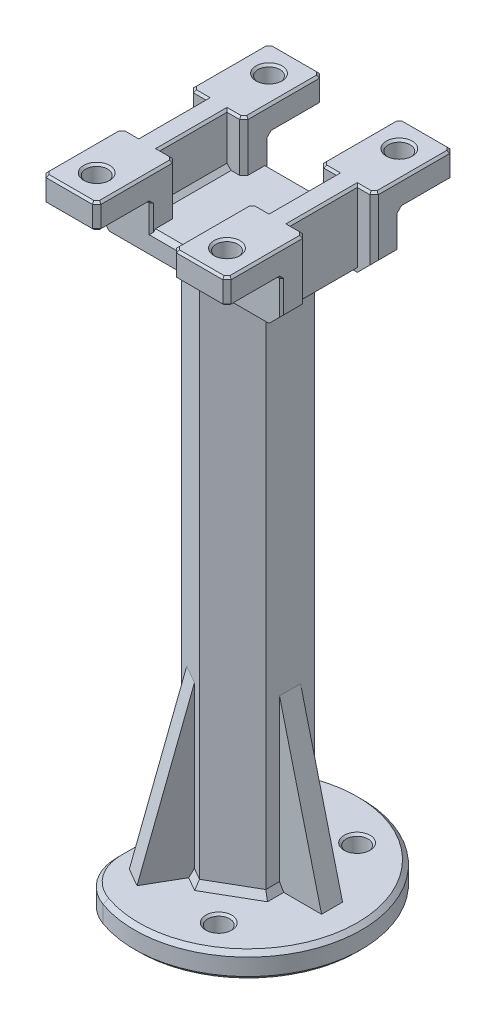
SolidWorks part; units mm, degrees
material "PET"
ref_plane "Front Plane" through (0, 0, 0) normal (0, 0, 1) x (1, 0, 0)
ref_plane "Top Plane" through (0, 0, 0) normal (0, 1, 0) x (1, 0, 0)
ref_plane "Right Plane" through (0, 0, 0) normal (1, 0, 0) x (0, 0, -1)
sketch "Sketch3" plane through (0, 0, 0) normal (0, 1, 0) x (1, 0, 0)
  circle A0 centre (0, 0) radius 27
  dimension "D1" = 54
extrude "Boss-Extrude1" add sketch "Sketch3" along normal blind 6
sketch "Sketch4" plane through (0, 6, 0) normal (0, 1, 0) x (1, 0, 0)
  line L0 (0, 0) -> (0, 11.547) construction
  line L1 (10, -5.7735) -> (10, 5.7735)
  line L2 (10, 5.7735) -> (0, 11.547)
  line L3 (0, 11.547) -> (-10, 5.7735)
  line L4 (-10, 5.7735) -> (-10, -5.7735)
  line L5 (-10, -5.7735) -> (0, -11.547)
  line L6 (0, -11.547) -> (10, -5.7735)
  circle A0 centre (0, 0) radius 10 construction
  dimension "D1" = 20
extrude "Boss-Extrude2" add sketch "Sketch4" along normal blind 126
sketch "Sketch13" plane through (0, 6, 0) normal (0, 1, 0) x (1, 0, 0)
  line L0 (-19, 0) -> (0, 0) construction
  line L1 (-19, 0) -> (9.5, 16.4545) construction
  line L2 (9.5, 16.4545) -> (9.5, -16.4545) construction
  line L3 (9.5, -16.4545) -> (-19, 0) construction
  circle A0 centre (-19, 0) radius 2.6 construction
  circle A1 centre (0, 0) radius 19 construction
  circle A2 centre (9.5, 16.4545) radius 2.6
  circle A3 centre (9.5, -16.4545) radius 2.6
  point P12 (0, 0)
  dimension "D2" = 38
  dimension "D3" = 5.2
  dimension "D1" = 3
extrude "Cut-Extrude5" cut sketch "Sketch13" against normal up to next
sketch "Sketch6" plane through (0, 0, 0) normal (0, 0, 1) x (1, 0, 0)
  line L0 (-22, 150) -> (-22, 132)
  line L1 (-22, 132) -> (0, 132)
  line L2 (0, 132) -> (22, 132)
  line L3 (22, 132) -> (22, 150)
  line L4 (22, 150) -> (9, 150)
  line L5 (9, 150) -> (9, 138)
  line L6 (9, 138) -> (-9, 138)
  line L7 (-9, 138) -> (-9, 150)
  line L8 (-9, 150) -> (-22, 150)
  line L10 (0, 0) -> (0, 132) construction
  line L11 (0, 132) -> (10, 132) construction
  dimension "D1" = 6
  dimension "D2" = 12
  dimension "D3" = 44
  dimension "D4" = 13
extrude "Boss-Extrude3" add sketch "Sketch6" along normal mid plane 28
sketch "Sketch10" plane through (0, 150, 0) normal (0, 1, 0) x (1, 0, 0)
  line L0 (-22, -14) -> (-22, 14) construction
  line L1 (-22, 8) -> (-18, 8)
  line L2 (-22, 8) -> (-22, -8)
  line L3 (-22, -8) -> (-18, -8)
  line L4 (-18, 8) -> (-18, -8)
  line L5 (-9, -14) -> (-9, 14) construction
  line L6 (-9, 8) -> (-13, 8)
  line L7 (-9, 8) -> (-9, -8)
  line L8 (-9, -8) -> (-13, -8)
  line L9 (-13, 8) -> (-13, -8)
  line L10 (9, -14) -> (9, 14) construction
  line L11 (9, 8) -> (13, 8)
  line L12 (9, 8) -> (9, -8)
  line L13 (9, -8) -> (13, -8)
  line L14 (13, 8) -> (13, -8)
  line L15 (22, -14) -> (22, 14) construction
  line L16 (22, 8) -> (18, 8)
  line L17 (22, 8) -> (22, -8)
  line L18 (22, -8) -> (18, -8)
  line L19 (18, 8) -> (18, -8)
  line L20 (0, 0) -> (-9, 0) construction
  line L21 (-9, 14) -> (-22, 14) construction
  dimension "D1" = 4
  dimension "D2" = 6
extrude "Cut-Extrude3" cut sketch "Sketch10" against normal up to surface (12 mm away) up to face at (0, 138, 0)
sketch "Sketch11" plane through (0, 138, 0) normal (0, 1, 0) x (1, 0, 0)
  line L0 (22, -8) -> (22, 8) construction
  line L1 (22, 8) -> (18, 8) construction
  line L2 (18, 8) -> (18, -8) construction
  line L3 (18, -8) -> (22, -8) construction
  line L4 (-22, 8) -> (-22, -8) construction
  line L5 (-22, -8) -> (-18, -8) construction
  line L6 (-18, -8) -> (-18, 8) construction
  line L7 (-18, 8) -> (-22, 8) construction
  line L8 (22, -8) -> (22, 8)
  line L9 (22, 8) -> (18, 8)
  line L10 (18, 8) -> (18, -8)
  line L11 (18, -8) -> (22, -8)
  line L12 (-22, 8) -> (-22, -8)
  line L13 (-22, -8) -> (-18, -8)
  line L14 (-18, -8) -> (-18, 8)
  line L15 (-18, 8) -> (-22, 8)
extrude "Cut-Extrude4" cut sketch "Sketch11" against normal up to next
sketch "Sketch12" plane through (0, 150, 0) normal (0, 1, 0) x (1, 0, 0)
  line L0 (-9, 14) -> (-22, 14) construction
  line L1 (-22, 14) -> (-9, 14)
  line L2 (-22, 14) -> (-22, 27)
  line L3 (-22, 27) -> (-9, 27)
  line L4 (-9, 14) -> (-9, 27)
  line L5 (-22, -14) -> (-9, -14)
  line L6 (-22, -14) -> (-22, -27)
  line L7 (-22, -27) -> (-9, -27)
  line L8 (-9, -14) -> (-9, -27)
  line L9 (9, -14) -> (22, -14)
  line L10 (9, -14) -> (9, -27)
  line L11 (9, -27) -> (22, -27)
  line L12 (22, -14) -> (22, -27)
  line L13 (9, 14) -> (22, 14)
  line L14 (9, 14) -> (9, 27)
  line L15 (9, 27) -> (22, 27)
  line L16 (22, 14) -> (22, 27)
  line L17 (-22, 8) -> (-22, 14) construction
  line L18 (-9, 8) -> (-9, 14) construction
  line L19 (22, 14) -> (9, 14) construction
  line L20 (-9, -14) -> (-22, -14) construction
  line L21 (22, -14) -> (9, -14) construction
  line L22 (22, -14) -> (22, -8) construction
  line L23 (-22, -14) -> (-22, -8) construction
  line L24 (-9, -14) -> (-9, -8) construction
  line L25 (9, -14) -> (9, -8) construction
  line L26 (22, 8) -> (22, 14) construction
  line L27 (9, 8) -> (9, 14) construction
  dimension "D1" = 13
extrude "Boss-Extrude4" add sketch "Sketch12" against normal blind 6
sketch "Sketch7" plane through (0, 150, 0) normal (0, 1, 0) x (1, 0, 0)
  line L0 (-22, 27) -> (-15.5, 20.5) construction
  line L2 (-15.5, 20.5) -> (-9, 27) construction
  line L4 (15.5, -20.5) -> (-15.5, -20.5) construction
  line L7 (15.5, -20.5) -> (15.5, 20.5) construction
  line L9 (15.5, 20.5) -> (-15.5, 20.5) construction
  line L11 (-15.5, -20.5) -> (-15.5, 20.5) construction
  line L12 (15.5, -20.5) -> (-15.5, 20.5) construction
  line L14 (15.5, 20.5) -> (-15.5, -20.5) construction
  circle A0 centre (-15.5, 20.5) radius 2.6
  circle A1 centre (-15.5, -20.5) radius 2.6
  circle A2 centre (15.5, -20.5) radius 2.6
  circle A3 centre (15.5, 20.5) radius 2.6
  point P0 (0, 0)
  dimension "D1" = 5.2
  dimension "D2" = 41
extrude "Cut-Extrude1" cut sketch "Sketch7" against normal up to next
sketch "Sketch19" plane through (0, 6, 0) normal (0, 1, 0) x (1, 0, 0)
  line L0 (-17, -20.9762) -> (-17, 20.9762)
  line L1 (-17, 20.9762) -> (-27, 20.9762)
  line L2 (-27, 20.9762) -> (-27, -20.9762)
  line L3 (-27, -20.9762) -> (-17, -20.9762)
  circle A0 centre (0, 0) radius 27 construction
  dimension "D1" = 10
extrude "Cut-Extrude6" cut sketch "Sketch19" against normal up to next
sketch "Sketch18" plane through (0, 0, 0) normal (0, 0, 1) x (1, 0, 0)
  line L0 (10, 46) -> (20, 6)
  line L1 (20, 6) -> (10, 6) construction
  line L2 (10, 6) -> (10, 46) construction
  line L3 (27, 6) -> (-17, 6) construction
  line L4 (10, 132) -> (10, 6) construction
  dimension "D1" = 20
  dimension "D2" = 40
rib "Rib3" sketch "Sketch18" sketch "Sketch18" thickness 5 extrusion direction parallel to sketch draft on no parameters "D1"=5
pattern_circular "CirPattern1" count 3 over 360 about axis through (0, 0, 0) along (0, 1, 0) of "Rib3"
fillet "Fillet1" radius 12 2 edges at (-17, 3, -20.9762) (-17, 3, 20.9762)
chamfer "Chamfer1" distance 4 angle 45 2 edges at (-22, 132, -11) (22, 132, 11)
chamfer "Chamfer2" distance 1 angle 60 15 edges at (5, 132, -8.6603) (-5, 132, -8.6603) (-10, 132, 0) (-5, 132, 8.6603) (10, 132, 0) (5, 132, 8.6603) (-1.4175, 6, -10.7286) (-8.5825, 6, -6.5919) (-10, 6, 0) (5, 6, -8.6603) (10, 6, 4.1368) (10, 6, -4.1368) (-8.5825, 6, 6.5919) (-1.4175, 6, 10.7286) (5, 6, 8.6603)
chamfer "Chamfer3" distance 1 angle 45 30 edges at (-22, 147, -27) (-9, 147, -27) (-22, 147, 27) (-9, 147, 27) (9, 147, 27) (22, 147, 27) (9, 147, -27) (22, 147, -27) (0, 138, -14) (-17, 6, 0) (0, 138, 14) (-17, 0, 0) (27, 6, 0) (-14.798, 6, -21.0703) (-14.798, 6, 21.0703) (27, 0, 0) (-14.798, 0, -21.0703) (-14.798, 0, 21.0703) (22, 143, -8) (0, 132, -14) (0, 132, 14) (-22, 143, -8) (-22, 143, 8) (22, 143, 8) (-13, 138, 0) (-9, 144, 8) (-9, 144, -8) (13, 138, 0) (9, 144, -8) (9, 144, 8)
chamfer "Chamfer4" distance 0.5 angle 45 84 edges at (-22, 140, -14) (-9, 144, -20) (-15.5, 144, -14) (-22, 140, 14) (-22, 144, 20) (-15.5, 144, 14) (9, 140.5, 14) (9, 144, 20) (15.5, 144, 14) (9, 140.5, -14) (22, 144, -20) (15.5, 144, -14) (15.5, 150, -17.9) (15.5, 144, -23.1) (15.5, 150, 23.1) (15.5, 144, 23.1) (-15.5, 150, 23.1) (-15.5, 144, 23.1) (-15.5, 150, -17.9) (-15.5, 144, -23.1) (9.5, 6, -13.8545) (9.5, 0, -13.8545) (9.5, 6, 19.0545) (9.5, 0, 19.0545) (-9, 140.5, -14) (-9, 140.5, 14) (22, 140, -14) (22, 140, 14) (-11.5, 150, -8) (11.5, 150, 8) (9, 150, 17.5) (15.5, 150, 27) (22, 150, 17.5) (19.5, 150, -8) (22, 150, -17.5) (15.5, 150, -27) (9, 150, -17.5) (21.5, 150, -26.5) (9.5, 150, -26.5) (9.5, 150, 26.5) (21.5, 150, 26.5) (21.5, 150, 8.5) (21.5, 150, -8.5) (9.5, 150, -8.5) (9.5, 150, 8.5) (9, 144, -20) (-9, 150, 17.5) (-9, 144, 20) (-19.5, 150, 8) (-22, 150, 17.5) (-15.5, 150, 27) (-9, 150, -17.5) (-15.5, 150, -27) (-22, 150, -17.5) (-9.5, 150, -26.5) (-21.5, 150, -26.5) (-21.5, 150, -8.5) (-21.5, 150, 8.5) (-21.5, 150, 26.5) (-9.5, 150, 26.5) (-9.5, 150, -8.5) (-9.5, 150, 8.5) (22, 144, 20) (15.5, 144, 27) (9.5, 144, 26.5) (21.5, 144, 26.5) (-15.5, 144, 27) (-21.5, 144, 26.5) (-9.5, 144, 26.5) (-22, 144, -20) (-15.5, 144, -27) (-9.5, 144, -26.5) (-21.5, 144, -26.5) (15.5, 144, -27) (21.5, 144, -26.5) (9.5, 144, -26.5) (-18, 150, 0) (-19.5, 150, -8) (-13, 150, 0) (-11.5, 150, 8) (13, 150, 0) (11.5, 150, -8) (18, 150, 0) (19.5, 150, 8)
